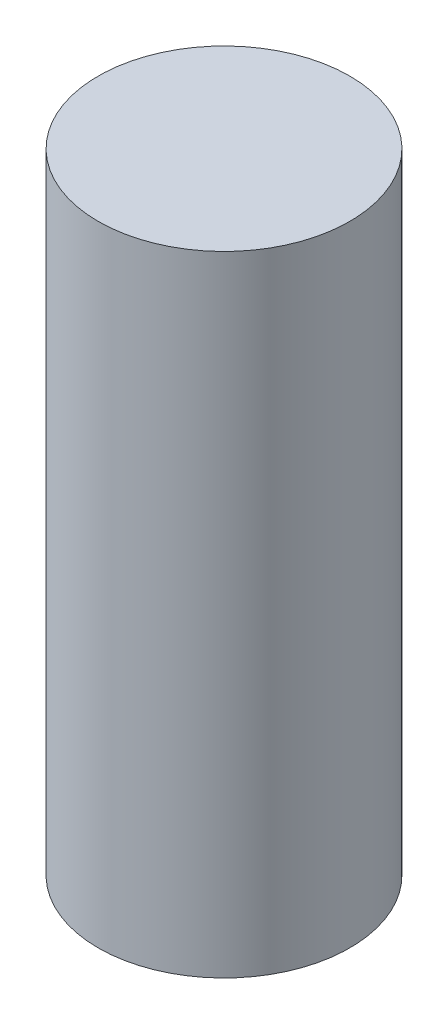
SolidWorks part; units mm, degrees
ref_plane "Front" through (0, 0, 0) normal (0, 0, 1) x (1, 0, 0)
ref_plane "Top" through (0, 0, 0) normal (0, 1, 0) x (1, 0, 0)
ref_plane "Right" through (0, 0, 0) normal (1, 0, 0) x (0, 0, -1)
sketch "Sketch1" plane through (0, 0, 0) normal (0, 1, 0) x (1, 0, 0)
  circle A0 centre (0, 0) radius 2
  dimension "D1" = 4
extrude "base" add sketch "Sketch1" along normal blind 10
